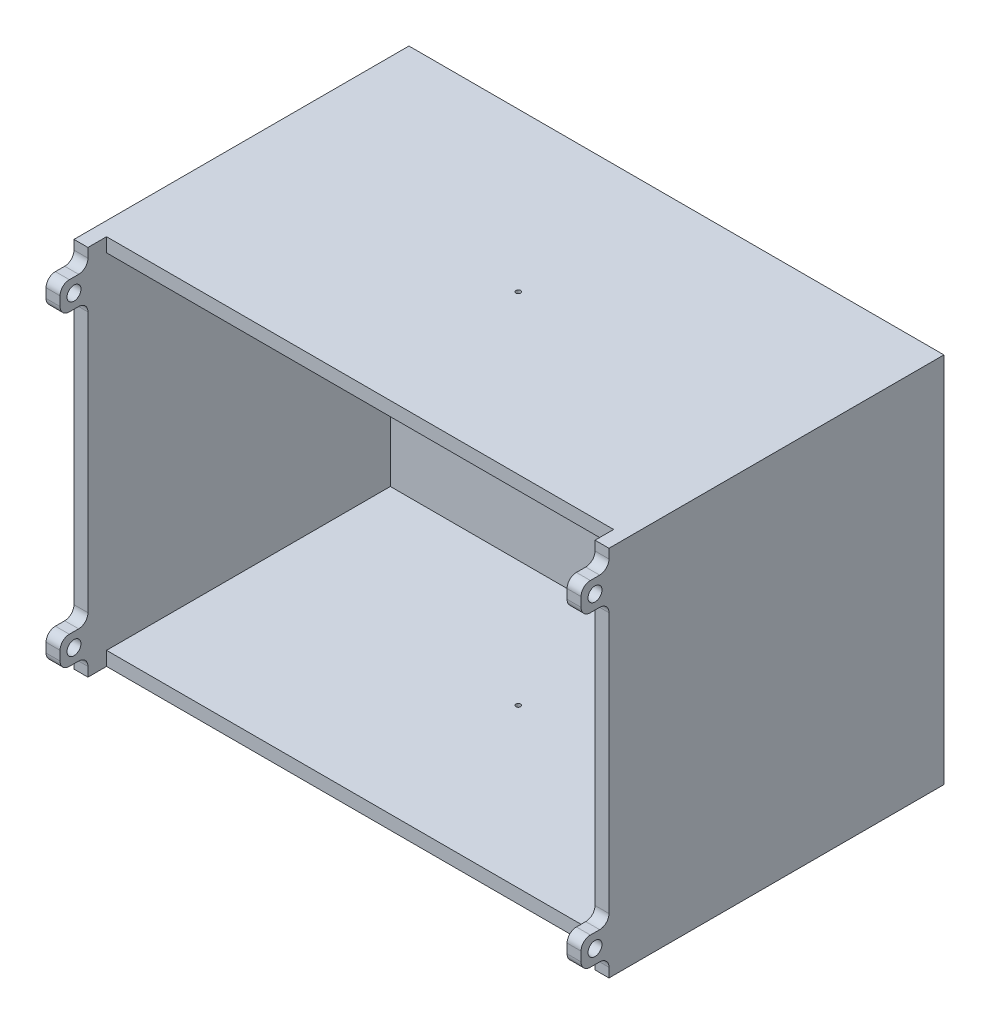
SolidWorks part; units mm, degrees
ref_plane "Front Plane" through (0, 0, 0) normal (1, 0, 0) x (0, 1, 0)
ref_plane "Top Plane" through (0, 0, 0) normal (0, 0, 1) x (0, 1, 0)
ref_plane "Right Plane" through (0, 0, 0) normal (0, 1, 0) x (-1, 0, 0)
sketch "Sketch1" plane through (0, 0, 0) normal (0, 0, 1) x (0, 1, 0)
  line L1 (-40, -57.5) -> (40, -57.5)
  line L2 (-40, -57.5) -> (-40, 57.5)
  line L3 (-40, 57.5) -> (40, 57.5)
  line L4 (40, -57.5) -> (40, 57.5)
  line L5 (-40, -57.5) -> (40, 57.5) construction
  line L6 (-40, 57.5) -> (40, -57.5) construction
  point P0 (0, 0)
  dimension "D1" = 115
  dimension "D2" = 80
extrude "Boss-Extrude1" add sketch "Sketch1" along normal blind 72
sketch "Sketch3" plane through (0, 0, 72) normal (0, 0, 1) x (1, 0, 0)
  line L0 (-57.5, 40) -> (-57.5, -40) construction
  line L1 (-54.5, -37) -> (54.5, -37)
  line L2 (-54.5, -37) -> (-54.5, 37)
  line L3 (-54.5, 37) -> (54.5, 37)
  line L4 (54.5, -37) -> (54.5, 37)
  line L5 (-54.5, -37) -> (54.5, 37) construction
  line L6 (-54.5, 37) -> (54.5, -37) construction
  line L7 (57.5, 40) -> (-57.5, 40) construction
  point P0 (0, 0)
  dimension "D1" = 3
  dimension "D2" = 3
extrude "Cut-Extrude1" cut sketch "Sketch3" against normal blind 65 and the other way through all
sketch "Sketch4" plane through (0, 0, 72) normal (0, 0, 1) x (1, 0, 0)
  line L0 (-54.5, 37) -> (-54.5, -37) construction
  line L1 (-54.5, 36) -> (-57.5, 36)
  line L2 (-54.5, 36) -> (-54.5, 30)
  line L3 (-54.5, 30) -> (-57.5, 30)
  line L4 (-57.5, 36) -> (-57.5, 30)
  line L5 (-57.5, 40) -> (-57.5, -40) construction
  line L6 (0.604, 0) -> (-54.5, 0) construction
  line L11 (0, 0) -> (0, 37) construction
  line L12 (54.5, 37) -> (-54.5, 37) construction
  line L13 (-54.5, -30) -> (-57.5, -30)
  line L14 (-57.5, -36) -> (-57.5, -30)
  line L15 (-54.5, -36) -> (-57.5, -36)
  line L16 (-54.5, -36) -> (-54.5, -30)
  line L17 (54.5, -36) -> (54.5, -30)
  line L18 (54.5, -36) -> (57.5, -36)
  line L19 (57.5, -36) -> (57.5, -30)
  line L20 (54.5, -30) -> (57.5, -30)
  line L21 (54.5, 30) -> (57.5, 30)
  line L22 (57.5, 36) -> (57.5, 30)
  line L23 (54.5, 36) -> (57.5, 36)
  line L24 (54.5, 36) -> (54.5, 30)
  dimension "D1" = 6
  dimension "D2" = 30
extrude "Boss-Extrude2" add sketch "Sketch4" along normal blind 6
sketch "Sketch5" plane through (0, 0, 72) normal (0, 0, 1) x (1, 0, 0)
  line L1 (-54.5, 40) -> (54.5, 40)
  line L2 (-54.5, 40) -> (-54.5, 37)
  line L3 (-54.5, 37) -> (54.5, 37)
  line L4 (54.5, 40) -> (54.5, 37)
  line L5 (54.5, 37) -> (-54.5, 37) construction
  line L6 (0, 0) -> (54.5, 0) construction
  line L7 (54.5, -30) -> (54.5, 30) construction
  line L8 (-54.5, -37) -> (54.5, -37)
  line L9 (54.5, -40) -> (54.5, -37)
  line L10 (-54.5, -40) -> (54.5, -40)
  line L11 (-54.5, -40) -> (-54.5, -37)
  line L12 (-54.5, 37) -> (-54.5, -37) construction
  line L13 (54.5, -37) -> (54.5, 37) construction
extrude "Cut-Extrude2" cut sketch "Sketch5" against normal blind 4
sketch "Sketch6" plane through (57.5, 0, 0) normal (1, 0, 0) x (0, 1, 0)
  line L0 (-36, 75) -> (-30, 75) construction
  line L1 (-36, 78) -> (-36, 72) construction
  line L2 (-30, 78) -> (-30, 72) construction
  line L3 (0, 0) -> (0, 72) construction
  line L4 (-30, 72) -> (30, 72) construction
  circle A0 centre (-33, 75) radius 1.5
  circle A1 centre (33, 75) radius 1.5
  dimension "D1" = 3
extrude "Cut-Extrude3" cut sketch "Sketch6" against normal through all both and the other way through all
fillet "Fillet1" radius 2 16 edges at (-56, -30, 72) (-56, -30, 78) (-56, -36, 78) (-56, -36, 72) (-56, 30, 72) (-56, 36, 78) (-56, 30, 78) (-56, 36, 72) (56, 36, 72) (56, 36, 78) (56, 30, 78) (56, 30, 72) (56, -36, 72) (56, -36, 78) (56, -30, 78) (56, -30, 72)
sketch "Sketch7" plane through (0, 40, 0) normal (0, 1, 0) x (-1, 0, 0)
  line L0 (0, 0) -> (0, 68) construction
  line L1 (-54.5, 68) -> (54.5, 68) construction
  circle A0 centre (0, 34) radius 0.5
  point P7 (0, 22.2833)
  point P8 (0, 25.2077)
  dimension "D1" = 1
extrude "Cut-Extrude4" cut sketch "Sketch7" against normal through all both and the other way through all
